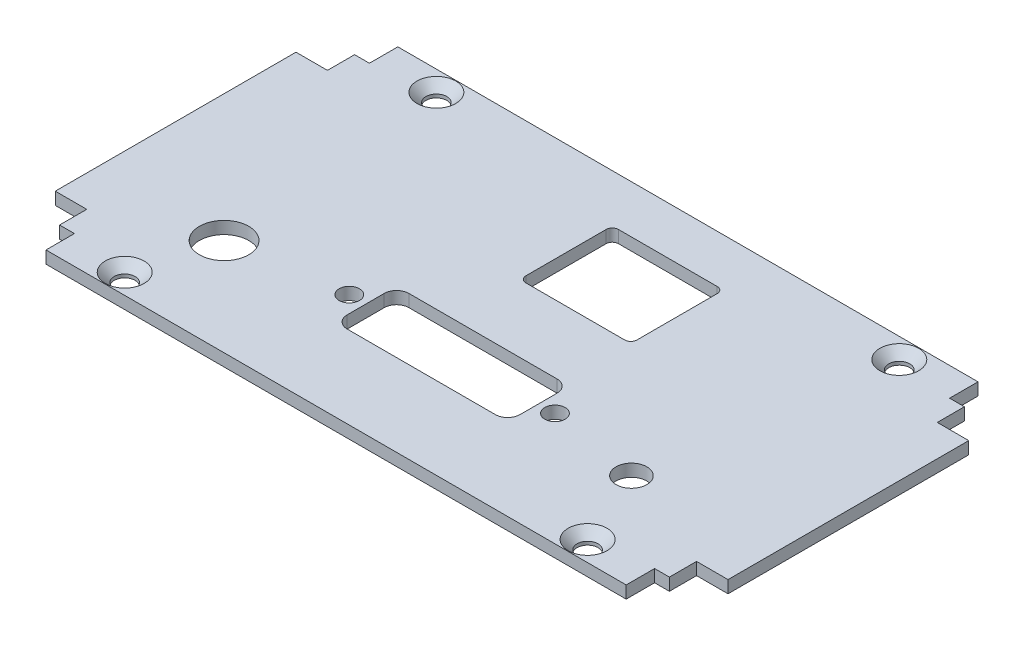
SolidWorks part; units mm, degrees
ref_plane "Спереди" through (0, 0, 0) normal (0, 0, 1) x (1, 0, 0)
ref_plane "Сверху" through (0, 0, 0) normal (0, 1, 0) x (1, 0, 0)
ref_plane "Справа" through (0, 0, 0) normal (1, 0, 0) x (0, 0, -1)
sketch "Эскиз1" plane through (0, 0, 0) normal (0, 1, 0) x (1, 0, 0)
  line L1 (-54.5, 28.5) -> (54.5, 28.5)
  line L2 (-54.5, 28.5) -> (-54.5, -28.5)
  line L3 (-54.5, -28.5) -> (54.5, -28.5)
  line L4 (54.5, 28.5) -> (54.5, -28.5)
  line L5 (-54.5, 28.5) -> (54.5, -28.5) construction
  line L6 (-54.5, -28.5) -> (54.5, 28.5) construction
  point P0 (0, 0)
  dimension "D1" = 109
  dimension "D2" = 57
extrude "Бобышка-Вытянуть1" add sketch "Эскиз1" along normal blind 2
sketch "Эскиз2" plane through (0, 2, 0) normal (0, 1, 0) x (1, 0, 0)
  line L0 (54.5, 19.5) -> (49.4, 19.5)
  line L1 (54.5, -28.5) -> (54.5, 28.5) construction
  line L2 (49.4, 19.5) -> (49.4, 23.9)
  line L3 (49.4, 23.9) -> (47, 23.9)
  line L4 (47, 23.9) -> (47, 28.5)
  line L5 (54.5, 28.5) -> (-54.5, 28.5) construction
  line M5 (54.5, -28.5) -> (54.5, 28.5)
  line M6 (54.5, 28.5) -> (-54.5, 28.5)
  dimension "D1" = 9
  dimension "D2" = 7.5
  dimension "D3" = 5.1
  dimension "D4" = 4.6
extrude "Вырез-Вытянуть1" cut sketch "Эскиз2" against normal through all contours L4 L3 L2 L0 M5 M6
mirror "Зеркальное отражение1" about plane through (0, 0, 0) normal (1, 0, 0) of "Вырез-Вытянуть1"
mirror "Зеркальное отражение2" about plane through (0, 0, 0) normal (0, 0, 1) of "Зеркальное отражение1", "Вырез-Вытянуть1"
sketch "Эскиз3" plane through (0, 2, 0) normal (0, 1, 0) x (1, 0, 0)
  line L1 (-54.5, 19.5) -> (-54.5, -19.5) construction
  line L3 (-47, -28.5) -> (47, -28.5) construction
  circle A0 centre (-33.9, -12.75) radius 4
  circle A1 centre (32.1, -12.75) radius 2.5
  dimension "D1" = 8
  dimension "D2" = 5
  dimension "D3" = 15.75
  dimension "D4" = 20.6
  dimension "D5" = 15.75
  dimension "D6" = 66
extrude "Вырез-Вытянуть2" cut sketch "Эскиз3" against normal through all
sketch "Эскиз4" plane through (0, 2, 0) normal (0, 1, 0) x (1, 0, 0)
  line L0 (0.5, -10.2) -> (14.5, -10.2) construction
  line L1 (-11.5, -5.2) -> (12.5, -5.2)
  line L2 (-13.5, -7.2) -> (-13.5, -13.2)
  line L3 (-11.5, -15.2) -> (12.5, -15.2)
  line L4 (14.5, -7.2) -> (14.5, -13.2)
  line L5 (-13.5, -5.2) -> (14.5, -15.2) construction
  line L6 (-13.5, -15.2) -> (14.5, -5.2) construction
  line L7 (0.5, -5.2) -> (0.5, -15.2) construction
  line L8 (-47, -28.5) -> (47, -28.5) construction
  line L9 (-54.5, 19.5) -> (-54.5, -19.5) construction
  arc A0 (-13.5, -13.2) -> (-11.5, -15.2) centre (-11.5, -13.2) ccw
  arc A1 (12.5, -15.2) -> (14.5, -13.2) centre (12.5, -13.2) ccw
  arc A2 (12.5, -5.2) -> (14.5, -7.2) centre (12.5, -7.2) cw
  arc A3 (-11.5, -5.2) -> (-13.5, -7.2) centre (-11.5, -7.2) ccw
  circle A4 centre (17.16, -10.2) radius 1.65
  circle A5 centre (-16.16, -10.2) radius 1.65
  point P0 (0.5, -10.2)
  dimension "D3" = 2
  dimension "D4" = 16.66
  dimension "D5" = 3.3
  dimension "D1" = 28
  dimension "D2" = 10
  dimension "D6" = 18.3
  dimension "D7" = 55
extrude "Вырез-Вытянуть3" cut sketch "Эскиз4" against normal blind 2
sketch "Эскиз5" plane through (0, 2, 0) normal (0, 1, 0) x (1, 0, 0)
  line L0 (47, 28.5) -> (-47, 28.5) construction
  line L1 (-4.5, 20.75) -> (13.5, 20.75)
  line L2 (-4.5, 20.75) -> (-4.5, 5.75)
  line L3 (-4.5, 5.75) -> (13.5, 5.75)
  line L4 (13.5, 20.75) -> (13.5, 5.75)
  line L5 (-4.5, 20.75) -> (13.5, 5.75) construction
  line L6 (-4.5, 5.75) -> (13.5, 20.75) construction
  line L7 (54.5, -19.5) -> (54.5, 19.5) construction
  point P0 (4.5, 13.25)
  dimension "D1" = 18
  dimension "D2" = 15
  dimension "D3" = 15.25
  dimension "D4" = 41
extrude "Вырез-Вытянуть4" cut sketch "Эскиз5" against normal through all
hole_wizard "Зенковка для винта с полупотайной головкой M31" positions "Эскиз8" profile "Эскиз6" countersink size "M3" standard "DIN" end condition up to next
sketch "Эскиз8" plane through (0, 2, 0) normal (0, 1, 0) x (1, 0, 0)
  line L0 (-54.5, 0) -> (54.5, 0) construction
  line L1 (-54.5, 19.5) -> (-54.5, -19.5) construction
  line L2 (54.5, -19.5) -> (54.5, 19.5) construction
  line L4 (0, 28.5) -> (0, -28.5) construction
  line L5 (47, 28.5) -> (-47, 28.5) construction
  line L6 (-47, -28.5) -> (47, -28.5) construction
  point P17 (37.5, 25.25)
  dimension "D1" = 25.25
  dimension "D2" = 37.5
sketch "Эскиз6" plane through (37.5, 2, -25.25) normal (1, 0, 0) x (0, 0, 1)
  line L0 (0, 0) -> (0, 2.001)
  line L1 (0, 2.001) -> (1.7, 2.001)
  line L2 (1.7, 2.001) -> (1.7, 1.45)
  line L3 (1.7, 1.45) -> (3.15, 0)
  line L5 (3.15, 0) -> (0, 0)
  line L6 (-1.7, 1.45) -> (-3.15, 0) construction
  line L11 (0, -6.35) -> (0, 107.95) construction
  dimension "Диаметр сквозного отверстия" = 3.4
  dimension "Глубина сквозного отверстия" = 2.001
  dimension "Диаметр передней зенковки" = 6.3
  dimension "Угол передней зенковки" = 90
mirror "Зеркальное отражение3" about plane through (0, 0, 0) normal (0, 0, 1) of "Зенковка для винта с полупотайной головкой M31"
mirror "Зеркальное отражение4" about plane through (0, 0, 0) normal (1, 0, 0) of "Зеркальное отражение3", "Зенковка для винта с полупотайной головкой M31"
fillet "Скругление1" radius 1 4 edges at (13.5, 1, -5.75) (-4.5, 1, -5.75) (-4.5, 1, -20.75) (13.5, 1, -20.75)
